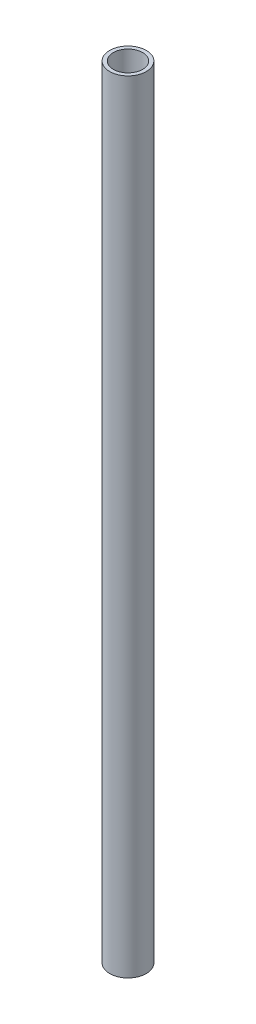
SolidWorks part; units mm, degrees
ref_plane "Front Plane" through (0, 0, 0) normal (0, 0, 1) x (1, 0, 0)
ref_plane "Top Plane" through (0, 0, 0) normal (0, 1, 0) x (1, 0, 0)
ref_plane "Right Plane" through (0, 0, 0) normal (1, 0, 0) x (0, 0, -1)
sketch "Sketch1" plane through (0, 0, 0) normal (0, 1, 0) x (1, 0, 0)
  circle A0 centre (0, 0) radius 4.7625
  circle A1 centre (0, 0) radius 3.81
  dimension "D1" = 9.525
  dimension "D2" = 7.62
extrude "Boss-Extrude1" add sketch "Sketch1" along normal blind 203.2
